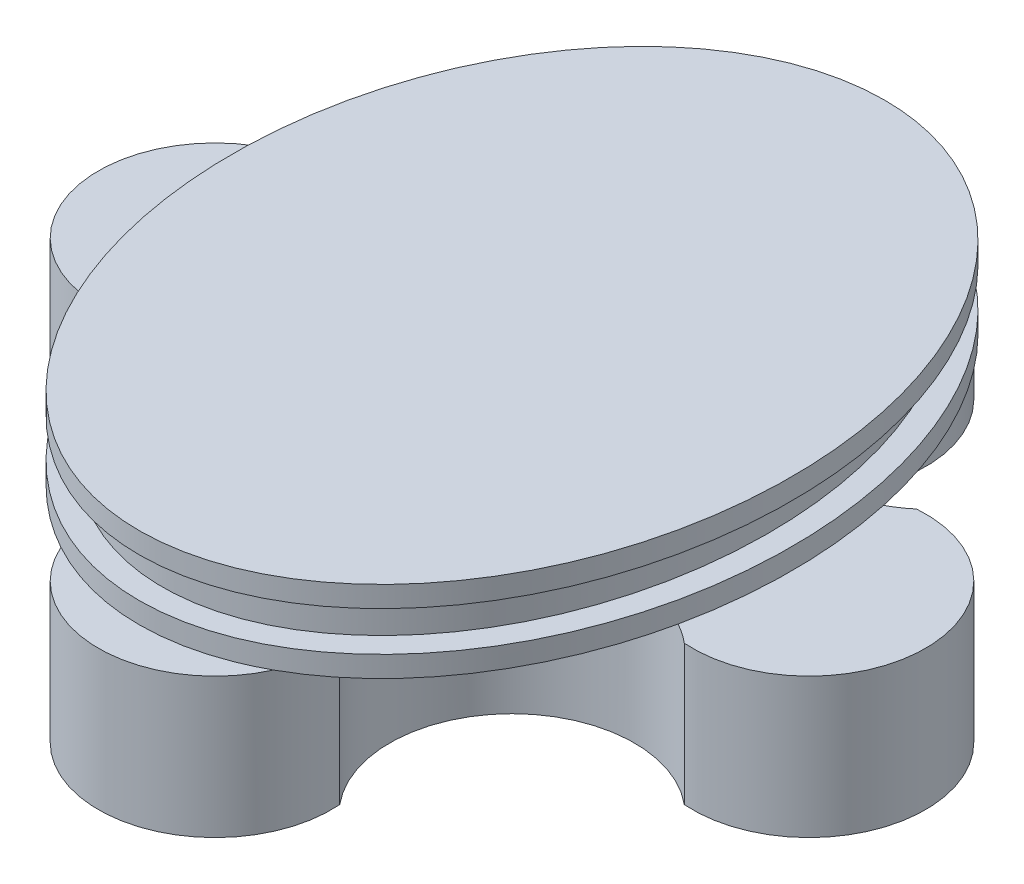
SolidWorks part; units mm, degrees
material "1060 Alloy"
ref_plane "Front" through (0, 0, 0) normal (0, 0, 1) x (1, 0, 0)
ref_plane "Top" through (0, 0, 0) normal (0, 1, 0) x (1, 0, 0)
ref_plane "Right" through (0, 0, 0) normal (1, 0, 0) x (0, 0, -1)
sketch "Sketch1" plane through (0, 0, 0) normal (0, 1, 0) x (1, 0, 0)
  line L0 (0, -55) -> (0, 55) construction
  line L1 (-55, 0) -> (55, 0) construction
  ellipse E0 centre (0, 0) end of major axis (0, 16) minor radius 12
  dimension "D1" = 24
  dimension "D2" = 32
  dimension "D3" = 0
  dimension "D4" = 0
extrude "Boss-Extrude1" add sketch "Sketch1" along normal blind 0.9
sketch "Sketch3" plane through (0, 0, 0) normal (0, -1, 0) x (-1, 0, 0)
  line L4 (0, 0.495) -> (0, -0.495) construction
  line L7 (-0.495, 0) -> (0.495, 0) construction
  circle A2 centre (0, 0) radius 12.75
  circle A3 centre (0, 12.75) radius 5
  circle A12 centre (-9.015, 9.0162) radius 5.25
  circle A13 centre (12.75, 0) radius 5
  circle A14 centre (0, -12.75) radius 5
  circle A15 centre (-12.75, 0) radius 5
  circle A16 centre (9.0162, 9.015) radius 5.25
  circle A17 centre (9.015, -9.0162) radius 5.25
  circle A18 centre (-9.0162, -9.015) radius 5.25
  point P17 (0, 0)
  point P22 (0, 0)
  point P25 (0, 0)
  dimension "D4" = 9.015
  dimension "D5" = 4
  dimension "D1" = 25.5
  dimension "D6" = 4
  dimension "D2" = 10
  dimension "D3" = 10.5
  dimension "D7" = 9.0162
  dimension "D8" = 9.015
  dimension "D9" = 12.75
  dimension "D10" = 12.75
extrude "Boss-Extrude2" add sketch "Sketch3" along normal blind 6
sketch "Sketch4" plane through (0, 0.9, 0) normal (0, 1, 0) x (1, 0, 0)
  circle A0 centre (0, 0) radius 3
  dimension "D1" = 6
extrude "Cut-Extrude1" cut sketch "Sketch4" against normal blind 10
sketch "Sketch5" plane through (0, 0.9, 0) normal (0, 1, 0) x (1, 0, 0)
  line L0 (0, -0.495) -> (0, 0.495) construction
  ellipse E0 centre (0, 0) end of major axis (0, 15) minor radius 11
  dimension "D1" = 30
  dimension "D2" = 22
extrude "Boss-Extrude3" add sketch "Sketch5" along normal blind 1.7
sketch "Sketch6" plane through (0, 2.6, 0) normal (0, 1, 0) x (1, 0, 0)
  line L0 (0, -0.495) -> (0, 0.495) construction
  ellipse E0 centre (0, 0) end of major axis (0, 16) minor radius 12
  dimension "D1" = 32
  dimension "D2" = 24
extrude "Boss-Extrude4" add sketch "Sketch6" along normal blind 0.9
